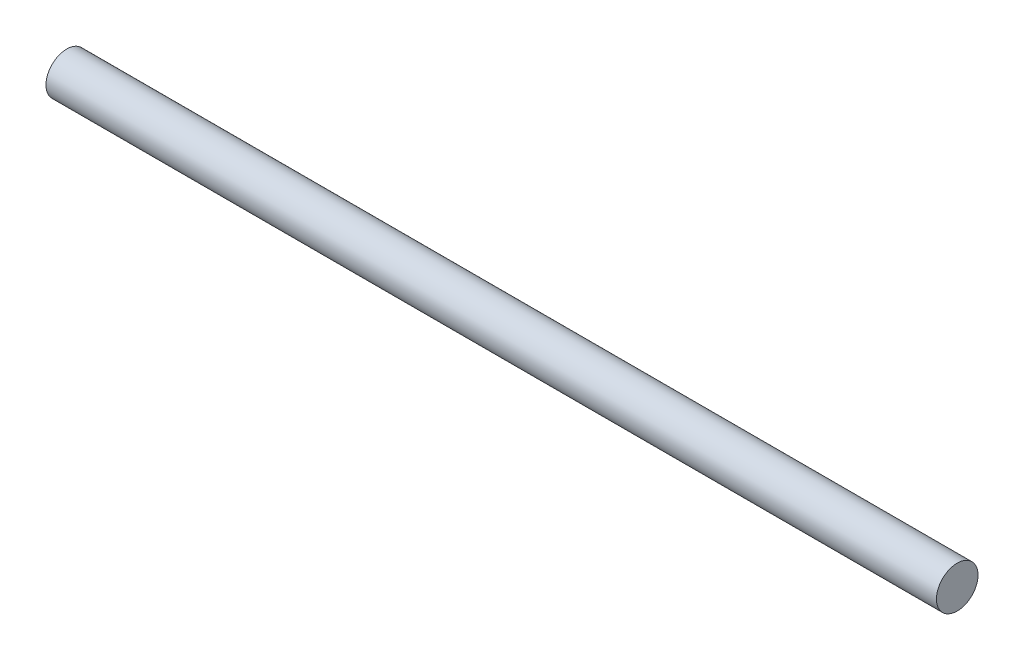
SolidWorks part; units mm, degrees
ref_plane "Front" through (0, 0, 0) normal (0, 0, 1) x (1, 0, 0)
ref_plane "Top" through (0, 0, 0) normal (0, 1, 0) x (1, 0, 0)
ref_plane "Right" through (0, 0, 0) normal (1, 0, 0) x (0, 0, -1)
sketch "Эскиз1" plane through (0, 0, 0) normal (1, 0, 0) x (0, 0, -1)
  circle A0 centre (0, 0) radius 14
  dimension "D1" = 28
extrude "Бобышка-Вытянуть1" add sketch "Эскиз1" along normal blind 600
